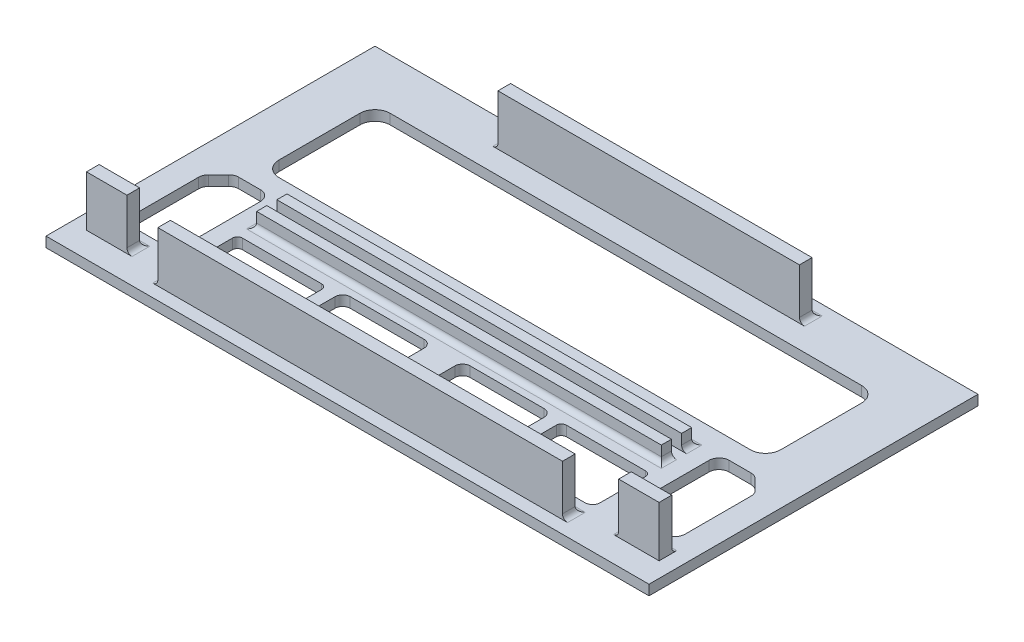
SolidWorks part; units mm, degrees
ref_plane "Front Plane" through (0, 0, 0) normal (0, 0, 1) x (1, 0, 0)
ref_plane "Top Plane" through (0, 0, 0) normal (0, 1, 0) x (1, 0, 0)
ref_plane "Right Plane" through (0, 0, 0) normal (1, 0, 0) x (0, 0, -1)
sketch "Sketch1" plane through (0, 0, 0) normal (0, 1, 0) x (1, 0, 0)
  line L1 (-59.6, -32.52) -> (59.6, -32.52)
  line L2 (-59.6, -32.52) -> (-59.6, 32.52)
  line L3 (-59.6, 32.52) -> (59.6, 32.52)
  line L4 (59.6, -32.52) -> (59.6, 32.52)
  line L5 (-59.6, -32.52) -> (59.6, 32.52) construction
  line L6 (-59.6, 32.52) -> (59.6, -32.52) construction
  point P0 (0, 0)
  dimension "D1" = 119.2
  dimension "D2" = 65.04
extrude "Boss-Extrude1" add sketch "Sketch1" along normal blind 2
ref_plane "Plane1" through (0, 0, 0) normal (-1, 0, 0) x (0, 0, 1)
sketch "Sketch2" plane through (0, 2, 0) normal (0, 1, 0) x (1, 0, 0)
  line L0 (-29.8, 29.52) -> (29.8, 29.52)
  line L1 (59.6, 32.52) -> (-59.6, 32.52) construction
  line L2 (59.6, -32.52) -> (59.6, 32.52) construction
  line L3 (59.6, -27.02) -> (59.6, -29.52)
  line L4 (29.8, 27.02) -> (-29.8, 27.02)
  line L5 (40, -4.48) -> (-40, -4.48)
  line L6 (40, -8.48) -> (40, -10.48)
  line L7 (-29.8, 29.52) -> (-29.8, 27.02)
  line L8 (29.8, 29.52) -> (29.8, 27.02)
  line L9 (-40, -4.48) -> (-40, -6.48)
  line L10 (-40, -6.48) -> (40, -6.48)
  line L11 (40, -6.48) -> (40, -4.48)
  line L12 (40, -10.48) -> (-40, -10.48)
  line L13 (-40, -10.48) -> (-40, -8.48)
  line L14 (-40, -8.48) -> (40, -8.48)
  line L15 (0, 1.1) -> (0, -1.1) construction
  point P16 (0, -10.48)
  dimension "D1" = 3
  dimension "D2" = 2.5
  dimension "D3" = 39
  dimension "D4" = 29.8
  dimension "D5" = 2
  dimension "D6" = 2
  dimension "D7" = 2
  dimension "D8" = 80
  dimension "D9" = 80
extrude "Boss-Extrude2" add sketch "Sketch2" along normal blind 10 contours L14 L13 L12 L6 | L10 L11 L5 L9 | L8 L0 L7 L4
fillet "Fillet1" radius 1 9 edges at (-29.8, 2, -28.27) (29.8, 2, -28.27) (0, 2, -29.52) (-40, 2, 5.48) (-40, 2, 9.48) (40, 2, 9.48) (40, 2, 5.48) (0, 2, 4.48) (0, 2, 10.48)
sketch "Sketch3" plane through (0, 12, 0) normal (0, 1, 0) x (1, 0, 0)
  line L0 (-40, -6.48) -> (40, -6.48) construction
  line L1 (40, -6.48) -> (40, -4.48) construction
  line L2 (40, -4.48) -> (-40, -4.48) construction
  line L3 (-40, -4.48) -> (-40, -6.48) construction
  line L4 (40, -8.48) -> (-40, -8.48) construction
  line L5 (-40, -8.48) -> (-40, -10.48) construction
  line L6 (-40, -10.48) -> (40, -10.48) construction
  line L7 (40, -10.48) -> (40, -8.48) construction
  line L8 (-40, -6.48) -> (40, -6.48)
  line L9 (40, -6.48) -> (40, -4.48)
  line L10 (40, -4.48) -> (-40, -4.48)
  line L11 (-40, -4.48) -> (-40, -6.48)
  line L12 (40, -8.48) -> (-40, -8.48)
  line L13 (-40, -8.48) -> (-40, -10.48)
  line L14 (-40, -10.48) -> (40, -10.48)
  line L15 (40, -10.48) -> (40, -8.48)
extrude "Cut-Extrude1" cut sketch "Sketch3" against normal blind 7
sketch "Sketch4" plane through (0, 2, 0) normal (0, 1, 0) x (1, 0, 0)
  line L0 (40, -30.02) -> (-40, -30.02)
  line L1 (-40, -30.02) -> (-40, -27.52)
  line L2 (-40, -27.52) -> (40, -27.52)
  line L3 (40, -27.52) -> (40, -30.02)
  line L4 (-59.6, -32.52) -> (59.6, -32.52) construction
  line L5 (0, 1.1) -> (0, -1.1) construction
  line L6 (48.6, -27.52) -> (56.6, -27.52)
  line L7 (56.6, -27.52) -> (56.6, -25.02)
  line L8 (56.6, -25.02) -> (48.6, -25.02)
  line L9 (48.6, -25.02) -> (48.6, -27.52)
  line L15 (59.6, -32.52) -> (59.6, 32.52) construction
  point P6 (0, -27.52)
  point P15 (52.6, -27.52)
  dimension "D1" = 2.5
  dimension "D2" = 2.5
  dimension "D3" = 80
  dimension "D4" = 2.5
  dimension "D6" = 3
  dimension "D7" = 8
extrude "Boss-Extrude3" add sketch "Sketch4" along normal blind 10
fillet "Fillet2" radius 1 5 edges at (-40, 2, 28.77) (48.6, 2, 26.27) (52.6, 2, 25.02) (40, 2, 28.77) (0, 2, 27.52)
mirror "Mirror1" about plane through (0, 0, 0) normal (-1, 0, 0) of "Boss-Extrude3"
fillet "Fillet3" radius 1 2 edges at (-52.6, 2, 25.02) (-48.6, 2, 26.27)
sketch "Sketch5" plane through (0, 2, 0) normal (0, 1, 0) x (1, 0, 0)
  line L0 (46.6, 22.52) -> (6.3115, 22.52)
  line L1 (6.3115, 22.52) -> (-46.6, 22.52)
  line L2 (-49.6, 19.52) -> (-49.6, 3.52)
  line L3 (-46.6, 0.52) -> (46.6, 0.52)
  line L4 (49.6, 3.52) -> (49.6, 19.52)
  line L5 (59.6, 32.52) -> (-59.6, 32.52) construction
  line L6 (59.6, -32.52) -> (59.6, 32.52) construction
  line L7 (-59.6, 32.52) -> (-59.6, -32.52) construction
  arc A0 (-49.6, 3.52) -> (-46.6, 0.52) centre (-46.6, 3.52) ccw
  arc A1 (-46.6, 22.52) -> (-49.6, 19.52) centre (-46.6, 19.52) ccw
  arc A2 (46.6, 22.52) -> (49.6, 19.52) centre (46.6, 19.52) cw
  arc A3 (46.6, 0.52) -> (49.6, 3.52) centre (46.6, 3.52) ccw
  dimension "D5" = 3
  dimension "D1" = 10
  dimension "D2" = 10
  dimension "D3" = 10
  dimension "D4" = 22
extrude "Cut-Extrude2" cut sketch "Sketch5" against normal blind 10
sketch "Sketch6" plane through (0, 2, 0) normal (0, 1, 0) x (1, 0, 0)
  line L3 (54.0142, -5.9408) -> (52.0453, -3.9719)
  line L4 (50.6311, -3.3862) -> (46.3278, -3.3862)
  line L5 (54.6, -7.3551) -> (54.6, -20.3979)
  line L6 (52.6, -22.3979) -> (46.3278, -22.3979)
  line L7 (44.3278, -20.3979) -> (44.3278, -5.3862)
  line L10 (39.8278, -13.4493) -> (24.2108, -13.4493)
  line L16 (4.044, -24.8936) -> (19.6609, -24.8936)
  line L17 (40.8278, -14.4493) -> (40.8278, -23.3936)
  line L18 (39.3278, -24.8936) -> (24.7108, -24.8936)
  line L19 (23.2108, -23.3936) -> (23.2108, -14.4493)
  line L21 (20.6609, -23.8936) -> (20.6609, -14.3214)
  line L22 (19.1609, -12.8214) -> (4.544, -12.8214)
  line L23 (3.044, -14.3214) -> (3.044, -23.8936)
  line L25 (59.6, -32.52) -> (59.6, 32.52) construction
  line L26 (0, -47.4967) -> (0, 52.968) construction
  line L29 (-4.044, -24.8936) -> (-19.6609, -24.8936)
  line L31 (-3.044, -14.3214) -> (-3.044, -23.8936)
  line L33 (-19.1609, -12.8214) -> (-4.544, -12.8214)
  line L34 (-20.6609, -23.8936) -> (-20.6609, -14.3214)
  line L37 (-39.3278, -24.8936) -> (-24.7108, -24.8936)
  line L39 (-39.8278, -13.4493) -> (-24.2108, -13.4493)
  line L40 (-23.2108, -14.4493) -> (-23.2108, -23.3936)
  line L42 (-40.8278, -23.3936) -> (-40.8278, -14.4493)
  line L43 (-44.3278, -5.3862) -> (-44.3278, -20.3979)
  line L44 (-50.6311, -3.3862) -> (-46.3278, -3.3862)
  line L45 (-54.0142, -5.9408) -> (-52.0453, -3.9719)
  line L46 (-54.6, -20.3979) -> (-54.6, -7.3551)
  line L51 (-52.6, -22.3979) -> (-46.3278, -22.3979)
  arc A1 (44.3278, -5.3862) -> (46.3278, -3.3862) centre (46.3278, -5.3862) cw
  arc A2 (52.0453, -3.9719) -> (50.6311, -3.3862) centre (50.6311, -5.3862) ccw
  arc A3 (54.6, -7.3551) -> (54.0142, -5.9408) centre (52.6, -7.3551) ccw
  arc A5 (46.3278, -22.3979) -> (44.3278, -20.3979) centre (46.3278, -20.3979) cw
  arc A8 (54.6, -20.3979) -> (52.6, -22.3979) centre (52.6, -20.3979) cw
  arc A10 (4.544, -12.8214) -> (3.044, -14.3214) centre (4.544, -14.3214) ccw
  arc A11 (20.6609, -14.3214) -> (19.1609, -12.8214) centre (19.1609, -14.3214) ccw
  arc A15 (24.7108, -24.8936) -> (23.2108, -23.3936) centre (24.7108, -23.3936) cw
  arc A16 (40.8278, -23.3936) -> (39.3278, -24.8936) centre (39.3278, -23.3936) cw
  arc A18 (3.044, -23.8936) -> (4.044, -24.8936) centre (4.044, -23.8936) ccw
  arc A19 (20.6609, -23.8936) -> (19.6609, -24.8936) centre (19.6609, -23.8936) cw
  arc A21 (40.8278, -14.4493) -> (39.8278, -13.4493) centre (39.8278, -14.4493) ccw
  arc A23 (24.2108, -13.4493) -> (23.2108, -14.4493) centre (24.2108, -14.4493) ccw
  arc A26 (-3.044, -23.8936) -> (-4.044, -24.8936) centre (-4.044, -23.8936) cw
  arc A27 (-20.6609, -23.8936) -> (-19.6609, -24.8936) centre (-19.6609, -23.8936) ccw
  arc A29 (-4.544, -12.8214) -> (-3.044, -14.3214) centre (-4.544, -14.3214) cw
  arc A31 (-20.6609, -14.3214) -> (-19.1609, -12.8214) centre (-19.1609, -14.3214) cw
  arc A35 (-40.8278, -23.3936) -> (-39.3278, -24.8936) centre (-39.3278, -23.3936) ccw
  arc A36 (-24.7108, -24.8936) -> (-23.2108, -23.3936) centre (-24.7108, -23.3936) ccw
  arc A37 (-24.2108, -13.4493) -> (-23.2108, -14.4493) centre (-24.2108, -14.4493) cw
  arc A40 (-40.8278, -14.4493) -> (-39.8278, -13.4493) centre (-39.8278, -14.4493) cw
  arc A41 (-44.3278, -5.3862) -> (-46.3278, -3.3862) centre (-46.3278, -5.3862) ccw
  arc A43 (-52.0453, -3.9719) -> (-50.6311, -3.3862) centre (-50.6311, -5.3862) cw
  arc A44 (-54.6, -7.3551) -> (-54.0142, -5.9408) centre (-52.6, -7.3551) cw
  arc A46 (-46.3278, -22.3979) -> (-44.3278, -20.3979) centre (-46.3278, -20.3979) ccw
  arc A49 (-54.6, -20.3979) -> (-52.6, -22.3979) centre (-52.6, -20.3979) ccw
  point P66 (3.044, -22.0111)
  point P71 (20.6609, -24.8936)
  point P74 (20.6609, -22.0111)
  dimension "D1" = 5
  dimension "D8" = 3.5
extrude "Cut-Extrude3" cut sketch "Sketch6" against normal blind 10
